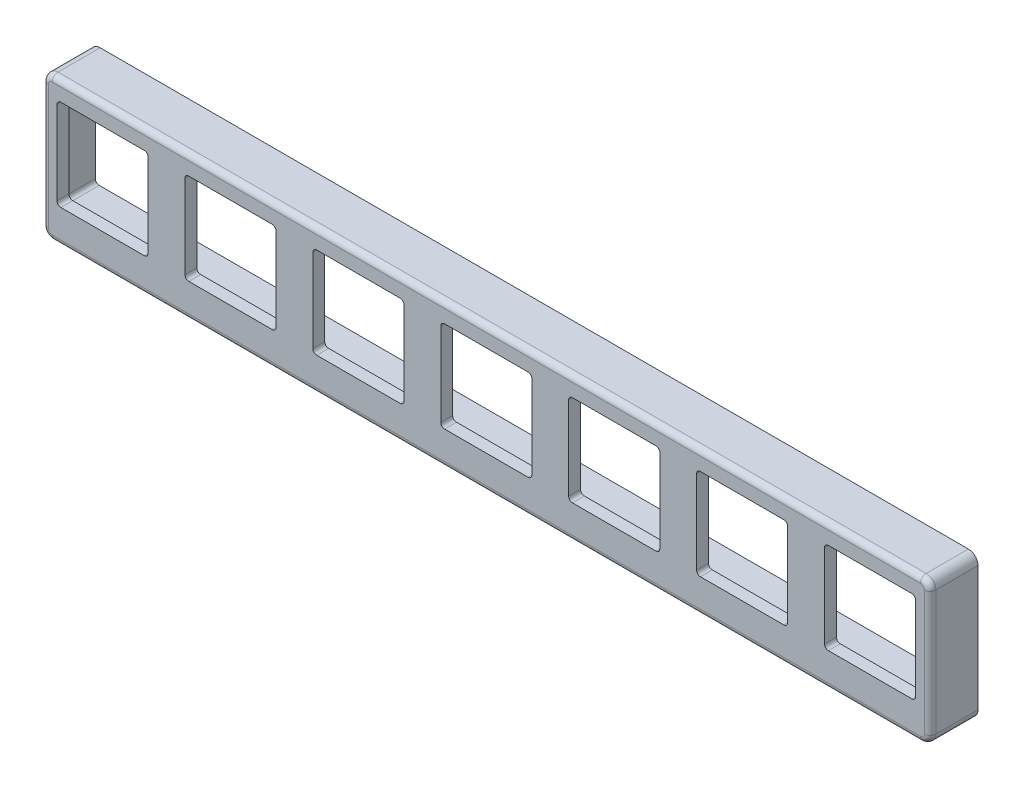
SolidWorks part; units mm, degrees
material "ABS PC"
ref_plane "Front Plane" through (0, 0, 0) normal (0, 0, 1) x (1, 0, 0)
ref_plane "Top Plane" through (0, 0, 0) normal (0, 1, 0) x (1, 0, 0)
ref_plane "Right Plane" through (0, 0, 0) normal (1, 0, 0) x (0, 0, -1)
sketch "Sketch1" plane through (0, 0, 0) normal (0, 0, 1) x (1, 0, 0)
  line L4 (-58.7375, -67.1355) -> (58.7375, -67.1355)
  line L5 (58.7375, -67.1355) -> (58.7375, -48.0855)
  line L6 (58.7375, -48.0855) -> (-58.7375, -48.0855)
  line L7 (-58.7375, -48.0855) -> (-58.7375, -67.1355)
  line L8 (-58.7375, -67.1355) -> (58.7375, -67.1355)
  line L9 (58.7375, -67.1355) -> (58.7375, -48.0855)
  line L10 (58.7375, -48.0855) -> (-58.7375, -48.0855)
  line L11 (-58.7375, -48.0855) -> (-58.7375, -67.1355)
  dimension "D1" = 0
extrude "Boss-Extrude1" add sketch "Sketch1" along normal up to surface (9.525 mm away)
sketch "Sketch2" plane through (0, 0, 0) normal (0, 0, 1) x (1, 0, 0)
  line L0 (35.56, -48.0855) -> (58.7375, -48.0855) construction
  line L1 (58.7375, -48.0855) -> (44.94, -39.2609) construction
  line L2 (38.1, -43.0055) -> (38.1, -45.5455) construction
  line L3 (-38.1, -45.5455) -> (-38.1, -43.0055) construction
  line L4 (-44.94, -39.2609) -> (-58.7375, -48.0855) construction
  line L5 (-58.7375, -48.0855) -> (-35.56, -48.0855) construction
  line L6 (35.56, -48.0855) -> (58.7375, -48.0855)
  line L7 (58.7375, -48.0855) -> (44.94, -39.2609)
  line L8 (38.1, -43.0055) -> (38.1, -45.5455)
  line L9 (-38.1, -45.5455) -> (-38.1, -43.0055)
  line L10 (-44.94, -39.2609) -> (-58.7375, -48.0855)
  line L11 (-58.7375, -48.0855) -> (-35.56, -48.0855)
  arc A0 (44.94, -39.2609) -> (38.1, -43.0055) centre (42.545, -43.0055) ccw construction
  arc A1 (35.56, -48.0855) -> (38.1, -45.5455) centre (35.56, -45.5455) ccw construction
  arc A2 (-38.1, -45.5455) -> (-35.56, -48.0855) centre (-35.56, -45.5455) ccw construction
  arc A3 (-38.1, -43.0055) -> (-44.94, -39.2609) centre (-42.545, -43.0055) ccw construction
  arc A4 (44.94, -39.2609) -> (38.1, -43.0055) centre (42.545, -43.0055) ccw
  arc A5 (35.56, -48.0855) -> (38.1, -45.5455) centre (35.56, -45.5455) ccw
  arc A6 (-38.1, -45.5455) -> (-35.56, -48.0855) centre (-35.56, -45.5455) ccw
  arc A7 (-38.1, -43.0055) -> (-44.94, -39.2609) centre (-42.545, -43.0055) ccw
extrude "Boss-Extrude2" add sketch "Sketch2" along normal up to surface (3.175 mm away)
hole_wizard "#6 Clearance Hole1" positions "Sketch4" profile "Sketch3" hole size "#6" standard "ANSI Inch" end condition through all
sketch "Sketch4" plane through (0, 0, 3.175) normal (0, 0, 1) x (1, 0, 0)
  point P0 (42.545, -43.0055)
  point P3 (-42.545, -43.0055)
sketch "Sketch3" plane through (42.545, -43.0055, 3.175) normal (1, 0, 0) x (0, -1, 0)
  line L0 (0, 0) -> (0, 3.175)
  line L1 (0, 3.175) -> (2.1526, 3.175)
  line L2 (2.1526, 3.175) -> (2.1526, 0)
  line L5 (2.1526, 0) -> (0, 0)
  line L11 (0, -6.35) -> (0, 107.95) construction
  dimension "Thru Hole Dia." = 4.3053
  dimension "Thru Hole Depth" = 3.175
sketch "Sketch5" plane through (0, 0, 9.525) normal (0, 0, 1) x (1, 0, 0)
  line L0 (56.8325, -50.5874) -> (44.7675, -50.5874) construction
  line L1 (44.7675, -50.5874) -> (44.7675, -62.6524) construction
  line L2 (44.7675, -62.6524) -> (56.8325, -62.6524) construction
  line L3 (56.8325, -62.6524) -> (56.8325, -50.5874) construction
  line L4 (39.8992, -62.6524) -> (39.8992, -50.5874) construction
  line L5 (39.8992, -50.5874) -> (27.8342, -50.5874) construction
  line L6 (27.8342, -50.5874) -> (27.8342, -62.6524) construction
  line L7 (27.8342, -62.6524) -> (39.8992, -62.6524) construction
  line L8 (10.9008, -50.5874) -> (10.9008, -62.6524) construction
  line L9 (10.9008, -62.6524) -> (22.9658, -62.6524) construction
  line L10 (22.9658, -62.6524) -> (22.9658, -50.5874) construction
  line L11 (22.9658, -50.5874) -> (10.9008, -50.5874) construction
  line L12 (6.0325, -50.5874) -> (-6.0325, -50.5874) construction
  line L13 (-6.0325, -50.5874) -> (-6.0325, -62.6524) construction
  line L14 (-6.0325, -62.6524) -> (6.0325, -62.6524) construction
  line L15 (6.0325, -62.6524) -> (6.0325, -50.5874) construction
  line L16 (-10.9008, -50.5874) -> (-22.9658, -50.5874) construction
  line L17 (-22.9658, -50.5874) -> (-22.9658, -62.6524) construction
  line L18 (-22.9658, -62.6524) -> (-10.9008, -62.6524) construction
  line L19 (-10.9008, -62.6524) -> (-10.9008, -50.5874) construction
  line L20 (-27.8342, -50.5874) -> (-39.8992, -50.5874) construction
  line L21 (-39.8992, -50.5874) -> (-39.8992, -62.6524) construction
  line L22 (-39.8992, -62.6524) -> (-27.8342, -62.6524) construction
  line L23 (-27.8342, -62.6524) -> (-27.8342, -50.5874) construction
  line L24 (-44.7675, -50.5874) -> (-56.8325, -50.5874) construction
  line L25 (-56.8325, -50.5874) -> (-56.8325, -62.6524) construction
  line L26 (-56.8325, -62.6524) -> (-44.7675, -62.6524) construction
  line L27 (-44.7675, -62.6524) -> (-44.7675, -50.5874) construction
  line L28 (56.8325, -50.5874) -> (44.7675, -50.5874)
  line L29 (44.7675, -50.5874) -> (44.7675, -62.6524)
  line L30 (44.7675, -62.6524) -> (56.8325, -62.6524)
  line L31 (56.8325, -62.6524) -> (56.8325, -50.5874)
  line L32 (39.8992, -62.6524) -> (39.8992, -50.5874)
  line L33 (39.8992, -50.5874) -> (27.8342, -50.5874)
  line L34 (27.8342, -50.5874) -> (27.8342, -62.6524)
  line L35 (27.8342, -62.6524) -> (39.8992, -62.6524)
  line L36 (10.9008, -50.5874) -> (10.9008, -62.6524)
  line L37 (10.9008, -62.6524) -> (22.9658, -62.6524)
  line L38 (22.9658, -62.6524) -> (22.9658, -50.5874)
  line L39 (22.9658, -50.5874) -> (10.9008, -50.5874)
  line L40 (6.0325, -50.5874) -> (-6.0325, -50.5874)
  line L41 (-6.0325, -50.5874) -> (-6.0325, -62.6524)
  line L42 (-6.0325, -62.6524) -> (6.0325, -62.6524)
  line L43 (6.0325, -62.6524) -> (6.0325, -50.5874)
  line L44 (-10.9008, -50.5874) -> (-22.9658, -50.5874)
  line L45 (-22.9658, -50.5874) -> (-22.9658, -62.6524)
  line L46 (-22.9658, -62.6524) -> (-10.9008, -62.6524)
  line L47 (-10.9008, -62.6524) -> (-10.9008, -50.5874)
  line L48 (-27.8342, -50.5874) -> (-39.8992, -50.5874)
  line L49 (-39.8992, -50.5874) -> (-39.8992, -62.6524)
  line L50 (-39.8992, -62.6524) -> (-27.8342, -62.6524)
  line L51 (-27.8342, -62.6524) -> (-27.8342, -50.5874)
  line L52 (-44.7675, -50.5874) -> (-56.8325, -50.5874)
  line L53 (-56.8325, -50.5874) -> (-56.8325, -62.6524)
  line L54 (-56.8325, -62.6524) -> (-44.7675, -62.6524)
  line L55 (-44.7675, -62.6524) -> (-44.7675, -50.5874)
extrude "Cut-Extrude1" cut sketch "Sketch5" against normal through all
sketch "Sketch7" plane through (0, 0, 0) normal (0, 0, -1) x (-1, 0, 0)
  line L56 (-56.8325, -62.6524) -> (-56.8325, -50.5874) construction
  line L57 (-58.1025, -49.3174) -> (58.1025, -49.3174)
  line L58 (-58.1025, -49.3174) -> (-58.1025, -63.9224)
  line L59 (-58.1025, -63.9224) -> (58.1025, -63.9224)
  line L60 (58.1025, -49.3174) -> (58.1025, -63.9224)
  line L61 (-58.1025, -49.3174) -> (58.1025, -63.9224) construction
  line L62 (-58.1025, -63.9224) -> (58.1025, -49.3174) construction
  line L63 (56.8325, -50.5874) -> (56.8325, -62.6524) construction
  line L64 (6.0325, -62.6524) -> (-6.0325, -62.6524) construction
  line L65 (-6.0325, -50.5874) -> (6.0325, -50.5874) construction
  point P4 (0, -56.6199)
  dimension "D1" = 1.27
  dimension "D2" = 1.27
  dimension "D3" = 1.27
  dimension "D4" = 1.27
extrude "Cut-Extrude2" cut sketch "Sketch7" against normal offset from surface (7.9502 mm away) 1.5748 up to face at (-50.8, -56.6199, 9.525)
sketch "Sketch8" plane through (0, 0, 0) normal (0, 0, -1) x (-1, 0, 0)
  line L0 (-58.7375, -67.1355) -> (-58.7375, -48.0855) construction
  line L1 (58.7375, -67.1355) -> (-58.7375, -67.1355)
  line L2 (58.7375, -67.1355) -> (58.7375, -38.5605)
  line L3 (58.7375, -38.5605) -> (-58.7375, -38.5605)
  line L4 (-58.7375, -67.1355) -> (-58.7375, -38.5605)
  line L5 (58.7375, -67.1355) -> (-58.7375, -38.5605) construction
  line L6 (58.7375, -38.5605) -> (-58.7375, -67.1355) construction
  arc A0 (-38.1, -43.0055) -> (-44.94, -39.2609) centre (-42.545, -43.0055) ccw construction
  point P4 (0, -52.848)
extrude "Cut-Extrude3" cut sketch "Sketch8" against normal up to surface (3.175 mm away) up to face at (-40.3924, -43.0055, 3.175)
fillet "Fillet2" radius 1.27 4 edges at (58.7375, -48.0855, 6.35) (-58.7375, -67.1355, 6.35) (-58.7375, -48.0855, 6.35) (58.7375, -67.1355, 6.35)
fillet "Fillet3" radius 0.762 8 edges at (-58.3655, -66.7635, 9.525) (-58.7375, -57.6105, 9.525) (-58.3655, -48.4575, 9.525) (0, -48.0855, 9.525) (58.3655, -48.4575, 9.525) (58.7375, -57.6105, 9.525) (58.3655, -66.7635, 9.525) (0, -67.1355, 9.525)
fillet "Fillet4" radius 0.508 8 edges at (-58.1025, -49.3174, 5.5626) (-58.1025, -63.9224, 5.5626) (58.1025, -63.9224, 5.5626) (58.1025, -49.3174, 5.5626) (-58.1025, -56.6199, 7.9502) (0, -63.9224, 7.9502) (58.1025, -56.6199, 7.9502) (0, -49.3174, 7.9502)
fillet "Fillet5" radius 0.508 28 edges at (56.8325, -50.5874, 8.7376) (56.8325, -62.6524, 8.7376) (44.7675, -62.6524, 8.7376) (44.7675, -50.5874, 8.7376) (39.8992, -62.6524, 8.7376) (27.8342, -62.6524, 8.7376) (27.8342, -50.5874, 8.7376) (39.8992, -50.5874, 8.7376) (10.9008, -50.5874, 8.7376) (22.9658, -50.5874, 8.7376) (10.9008, -62.6524, 8.7376) (6.0325, -50.5874, 8.7376) (6.0325, -62.6524, 8.7376) (-6.0325, -62.6524, 8.7376) (-6.0325, -50.5874, 8.7376) (-10.9008, -50.5874, 8.7376) (-10.9008, -62.6524, 8.7376) (-22.9658, -62.6524, 8.7376) (-22.9658, -50.5874, 8.7376) (-27.8342, -50.5874, 8.7376) (-27.8342, -62.6524, 8.7376) (-39.8992, -62.6524, 8.7376) (-39.8992, -50.5874, 8.7376) (-44.7675, -50.5874, 8.7376) (-44.7675, -62.6524, 8.7376) (-56.8325, -62.6524, 8.7376) (-56.8325, -50.5874, 8.7376) (22.9658, -62.6524, 8.7376)
